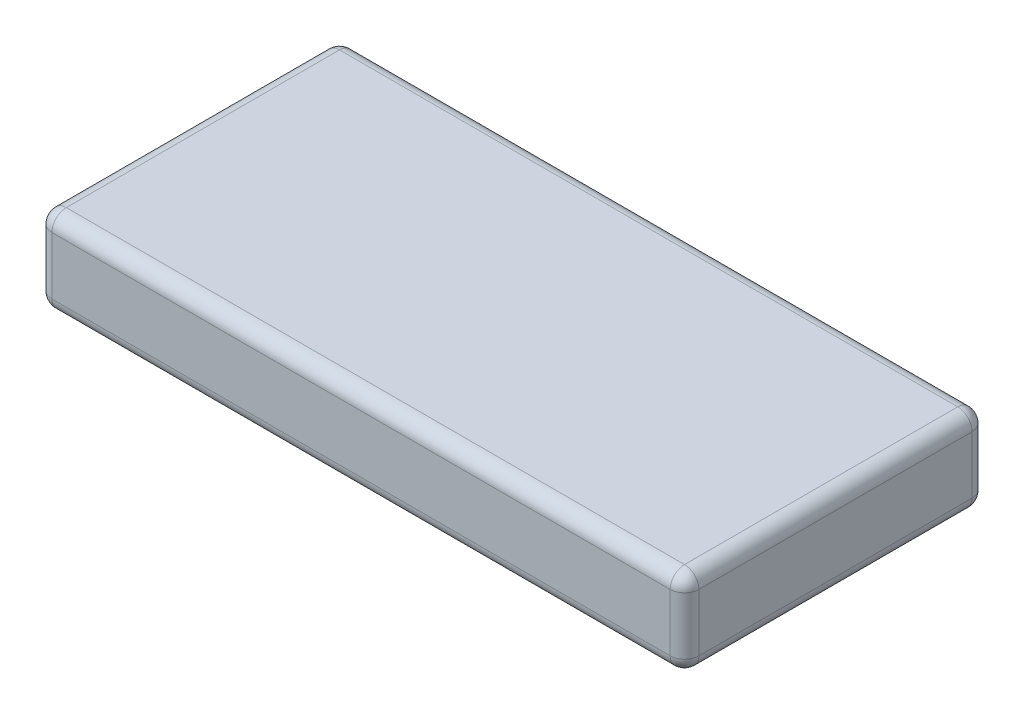
SolidWorks part; units mm, degrees
ref_plane "Front Plane" through (0, 0, 0) normal (0, 0, 1) x (1, 0, 0)
ref_plane "Top Plane" through (0, 0, 0) normal (0, 1, 0) x (1, 0, 0)
ref_plane "Right Plane" through (0, 0, 0) normal (1, 0, 0) x (0, 0, -1)
sketch "Sketch1" plane through (0, 0, 0) normal (0, 1, 0) x (1, 0, 0)
  line L1 (0, 0) -> (171.45, 0)
  line L2 (0, 0) -> (0, 80.01)
  line L3 (0, 80.01) -> (171.45, 80.01)
  line L4 (171.45, 0) -> (171.45, 80.01)
  dimension "D1" = 80.01
  dimension "D2" = 171.45
extrude "Boss-Extrude1" add sketch "Sketch1" along normal blind 22.86
fillet "Fillet1" radius 3.81 12 edges at (171.45, 11.43, -80.01) (171.45, 0, -40.005) (85.725, 0, -80.01) (0, 11.43, -80.01) (0, 0, -40.005) (85.725, 22.86, -80.01) (171.45, 22.86, -40.005) (0, 22.86, -40.005) (0, 11.43, 0) (85.725, 22.86, 0) (171.45, 11.43, 0) (85.725, 0, 0)
